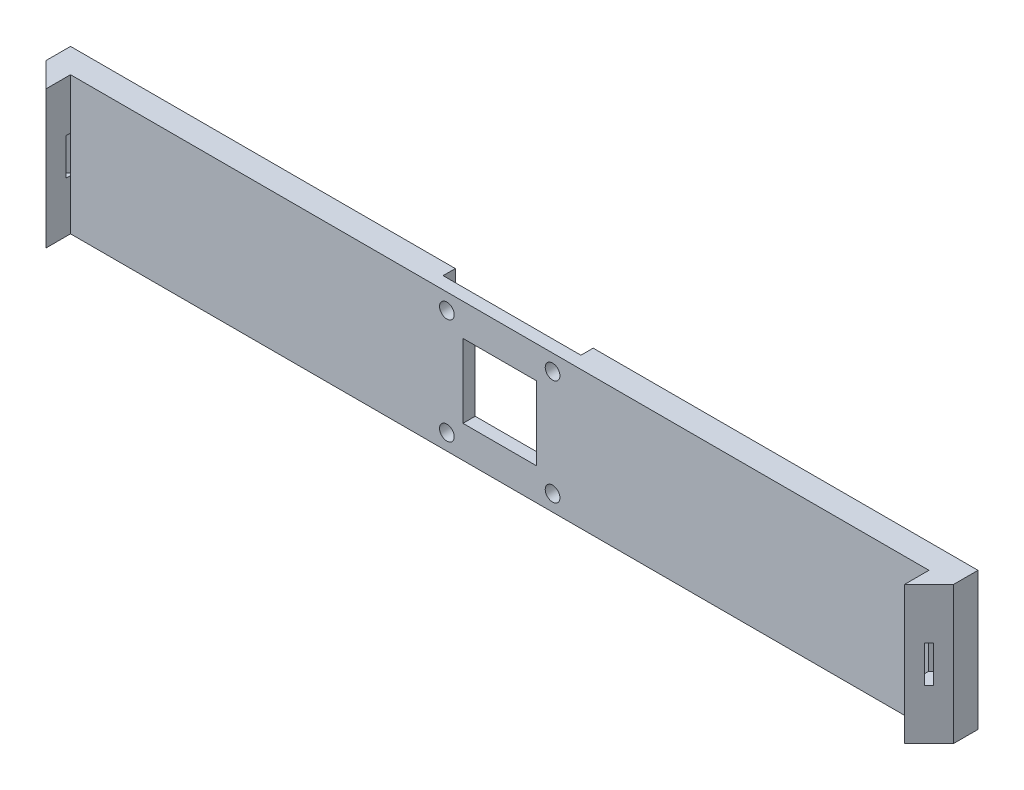
SolidWorks part; units mm, degrees
ref_plane "Front Plane" through (0, 0, 0) normal (0, 0, 1) x (1, 0, 0)
ref_plane "Top Plane" through (0, 0, 0) normal (0, 1, 0) x (1, 0, 0)
ref_plane "Right Plane" through (0, 0, 0) normal (1, 0, 0) x (0, 0, -1)
sketch "Sketch1" plane through (0, 0, 0) normal (0, 0, 1) x (1, 0, 0)
  line L1 (-175, -28.1) -> (175, -28.1)
  line L2 (-175, -28.1) -> (-175, 28.1)
  line L3 (-175, 28.1) -> (175, 28.1)
  line L4 (175, -28.1) -> (175, 28.1)
  line L5 (-175, -28.1) -> (175, 28.1) construction
  line L6 (-175, 28.1) -> (175, -28.1) construction
  point P0 (0, 0)
extrude "Boss-Extrude1" add sketch "Sketch1" along normal blind 10
sketch "Sketch2" plane through (0, 0, 10) normal (0, 0, 1) x (1, 0, 0)
  line L2 (175, 28.1) -> (-175, 28.1) construction
  line L3 (-28.1, -28.1) -> (28.1, -28.1)
  line L4 (-28.1, -28.1) -> (-28.1, 28.1)
  line L5 (-28.1, 28.1) -> (28.1, 28.1)
  line L6 (28.1, -28.1) -> (28.1, 28.1)
  point P8 (0, 0)
extrude "Cut-Extrude1" cut sketch "Sketch2" against normal blind 5
sketch "Sketch3" plane through (175, 0, 0) normal (1, 0, 0) x (0, 0, -1)
  line L1 (-10, 28.1) -> (0, 28.1)
  line L2 (-10, 28.1) -> (-10, -28.1)
  line L3 (-10, -28.1) -> (0, -28.1)
  line L4 (0, 28.1) -> (0, -28.1)
extrude "Boss-Extrude2" add sketch "Sketch3" along normal blind 10
sketch "Sketch4" plane through (0, 0, 10) normal (0, 0, 1) x (1, 0, 0)
  line L0 (28.1, -28.1) -> (185, -28.1) construction
  line L1 (185, 28.1) -> (175, 28.1)
  line L2 (185, 28.1) -> (185, -28.1)
  line L3 (185, -28.1) -> (175, -28.1)
  line L4 (175, 28.1) -> (175, -28.1)
extrude "Boss-Extrude3" add sketch "Sketch4" along normal blind 10
sketch "Sketch5" plane through (0, 28.1, 0) normal (0, 1, 0) x (1, 0, 0)
  line L0 (175, -20) -> (185, -10)
  line L1 (185, 0) -> (185, -20) construction
  line L2 (185, -10) -> (185, -20)
  line L3 (185, -20) -> (175, -20)
extrude "Cut-Extrude2" cut sketch "Sketch5" against normal blind 56.2
sketch "Sketch6" plane through (-175, 0, 0) normal (-1, 0, 0) x (0, 0, 1)
  line L1 (0, -28.1) -> (10, -28.1)
  line L2 (0, -28.1) -> (0, 28.1)
  line L3 (0, 28.1) -> (10, 28.1)
  line L4 (10, -28.1) -> (10, 28.1)
extrude "Boss-Extrude4" add sketch "Sketch6" along normal blind 10
sketch "Sketch7" plane through (0, 0, 10) normal (0, 0, 1) x (1, 0, 0)
  line L0 (-28.1, 28.1) -> (-185, 28.1) construction
  line L1 (-185, -28.1) -> (-175, -28.1)
  line L2 (-185, -28.1) -> (-185, 28.1)
  line L3 (-185, 28.1) -> (-175, 28.1)
  line L4 (-175, -28.1) -> (-175, 28.1)
extrude "Boss-Extrude5" add sketch "Sketch7" along normal blind 10
sketch "Sketch8" plane through (0, 28.1, 0) normal (0, 1, 0) x (1, 0, 0)
  line L0 (-175, -20) -> (-185, -10)
  line L1 (-185, -20) -> (-185, 0) construction
  line L2 (-185, -10) -> (-185, -20)
  line L3 (-185, -20) -> (-175, -20)
extrude "Cut-Extrude3" cut sketch "Sketch8" against normal blind 56.2
sketch "Sketch9" plane through (0, 0, 5) normal (0, 0, 1) x (1, 0, 0)
  line L3 (-15, -15) -> (15, -15)
  line L4 (-15, -15) -> (-15, 15)
  line L5 (-15, 15) -> (15, 15)
  line L6 (15, -15) -> (15, 15)
  point P4 (0, 0)
extrude "Cut-Extrude4" cut sketch "Sketch9" against normal blind 5
sketch "Sketch10" plane through (0, 0, 5) normal (0, 0, 1) x (1, 0, 0)
  circle A2 centre (21.55, 21.55) radius 3
  circle A3 centre (-21.55, -21.55) radius 3
  circle A4 centre (-21.55, 21.55) radius 3
  circle A5 centre (21.55, -21.55) radius 3
extrude "Cut-Extrude5" cut sketch "Sketch10" against normal blind 5
sketch "Sketch11" plane through (97.5, 0, 97.5) normal (0.7071, 0, 0.7071) x (0.7071, 0, -0.7071)
  line L3 (117.9226, -7.5) -> (115.4226, -7.5)
  line L4 (117.9226, -7.5) -> (117.9226, 7.5)
  line L5 (117.9226, 7.5) -> (115.4226, 7.5)
  line L6 (115.4226, -7.5) -> (115.4226, 7.5)
  line L7 (117.9226, -7.5) -> (115.4226, 7.5) construction
  line L8 (117.9226, 7.5) -> (115.4226, -7.5) construction
  point P6 (116.6726, 0)
  point P14 (116.6726, 0)
extrude "Cut-Extrude6" cut sketch "Sketch11" against normal blind 7
sketch "Sketch12" plane through (-97.5, 0, 97.5) normal (-0.7071, 0, 0.7071) x (0.7071, 0, 0.7071)
  line L2 (-117.9226, 7.5) -> (-115.4226, 7.5)
  line L3 (-117.9226, 7.5) -> (-117.9226, -7.5)
  line L4 (-117.9226, -7.5) -> (-115.4226, -7.5)
  line L5 (-115.4226, 7.5) -> (-115.4226, -7.5)
  line L6 (-117.9226, 7.5) -> (-115.4226, -7.5) construction
  line L7 (-117.9226, -7.5) -> (-115.4226, 7.5) construction
  point P4 (-116.6726, 0)
extrude "Cut-Extrude8" cut sketch "Sketch12" against normal blind 7
sketch "Sketch14" plane through (0, 0, 5) normal (0, 0, 1) x (1, 0, 0)
  line L0 (28.1, 28.1) -> (-28.1, 28.1) construction
  line L1 (-28.1, -28.1) -> (28.1, -28.1)
  line L2 (-28.1, -28.1) -> (-28.1, 28.1)
  line L3 (-28.1, 28.1) -> (28.1, 28.1)
  line L4 (28.1, -28.1) -> (28.1, 28.1)
  line L5 (-28.1, -28.1) -> (28.1, 28.1) construction
  line L6 (-28.1, 28.1) -> (28.1, -28.1) construction
  line L8 (-15, 15) -> (15, 15)
  line L9 (-15, 15) -> (-15, -15)
  line L10 (-15, -15) -> (15, -15)
  line L11 (15, 15) -> (15, -15)
  circle A0 centre (-21.55, 21.55) radius 3
  circle A1 centre (21.55, 21.55) radius 3
  circle A2 centre (21.55, -21.55) radius 3
  circle A3 centre (-21.55, -21.55) radius 3
  point P0 (0, 0)
extrude "Boss-Extrude7" add sketch "Sketch14" along normal blind 5
sketch "Sketch15" plane through (0, 0, 0) normal (0, 0, -1) x (-1, 0, 0)
  line L1 (-185, 28.1) -> (185, 28.1) construction
  line L3 (-28.1, -28.1) -> (28.1, -28.1)
  line L4 (-28.1, -28.1) -> (-28.1, 28.1)
  line L5 (-28.1, 28.1) -> (28.1, 28.1)
  line L6 (28.1, -28.1) -> (28.1, 28.1)
  line L7 (-28.1, -28.1) -> (28.1, 28.1) construction
  line L8 (-28.1, 28.1) -> (28.1, -28.1) construction
extrude "Cut-Extrude9" cut sketch "Sketch15" against normal blind 5
